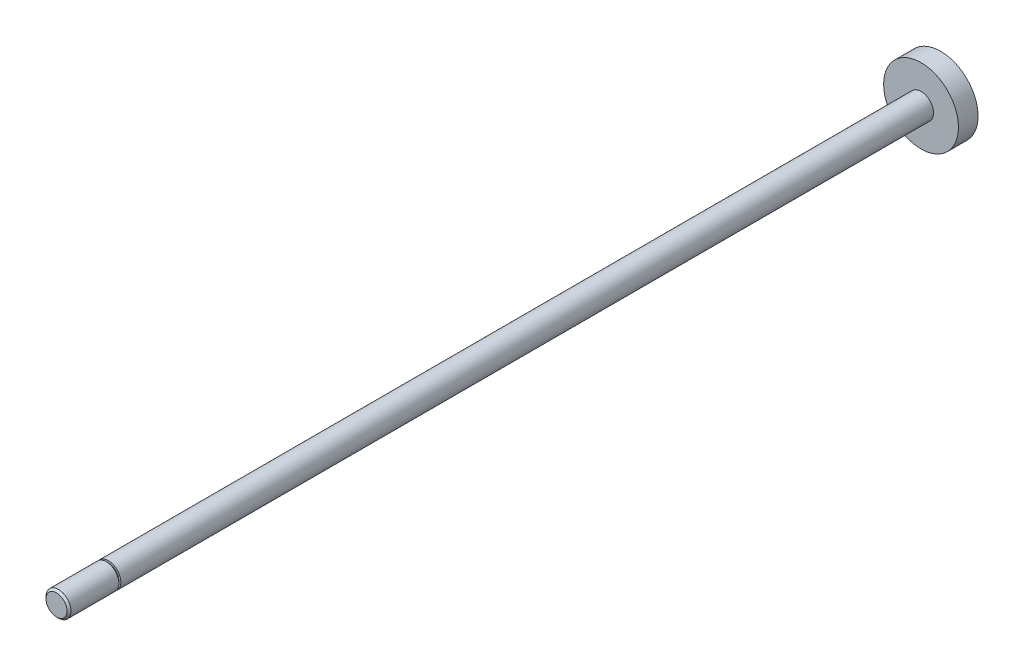
SolidWorks part; units mm, degrees
material "Alloy Steel"
ref_plane "Front Plane" through (0, 0, 0) normal (0, 0, 1) x (1, 0, 0)
ref_plane "Top Plane" through (0, 0, 0) normal (0, 1, 0) x (1, 0, 0)
ref_plane "Right Plane" through (0, 0, 0) normal (1, 0, 0) x (0, 0, -1)
ref_plane "Plane1" through (0, 0, 0) normal (0, -1, 0) x (1, 0, 0)
sketch "Sketch1" plane through (0, 0, 0) normal (0, -1, 0) x (1, 0, 0)
  line L0 (2.675, 146.431) -> (0, 146.431)
  line L1 (0, 146.431) -> (0, -78.7)
  line L2 (0, -78.7) -> (9.525, -78.7)
  line L3 (9.525, -78.7) -> (9.525, -73.7)
  line L4 (9.525, -73.7) -> (3.175, -73.7)
  line L5 (3.175, -73.7) -> (3.175, 133.231)
  line L6 (3.175, 133.231) -> (2.675, 133.231)
  line L7 (2.675, 133.231) -> (2.675, 133.731)
  line L8 (2.675, 133.731) -> (3.175, 133.731)
  line L9 (3.175, 133.731) -> (3.175, 145.931)
  line L10 (3.175, 145.931) -> (2.675, 146.431)
  line L11 (0, 146.431) -> (0, -78.7) construction
revolve "Revolve1" add sketch "Sketch1" angle 360 about L11
